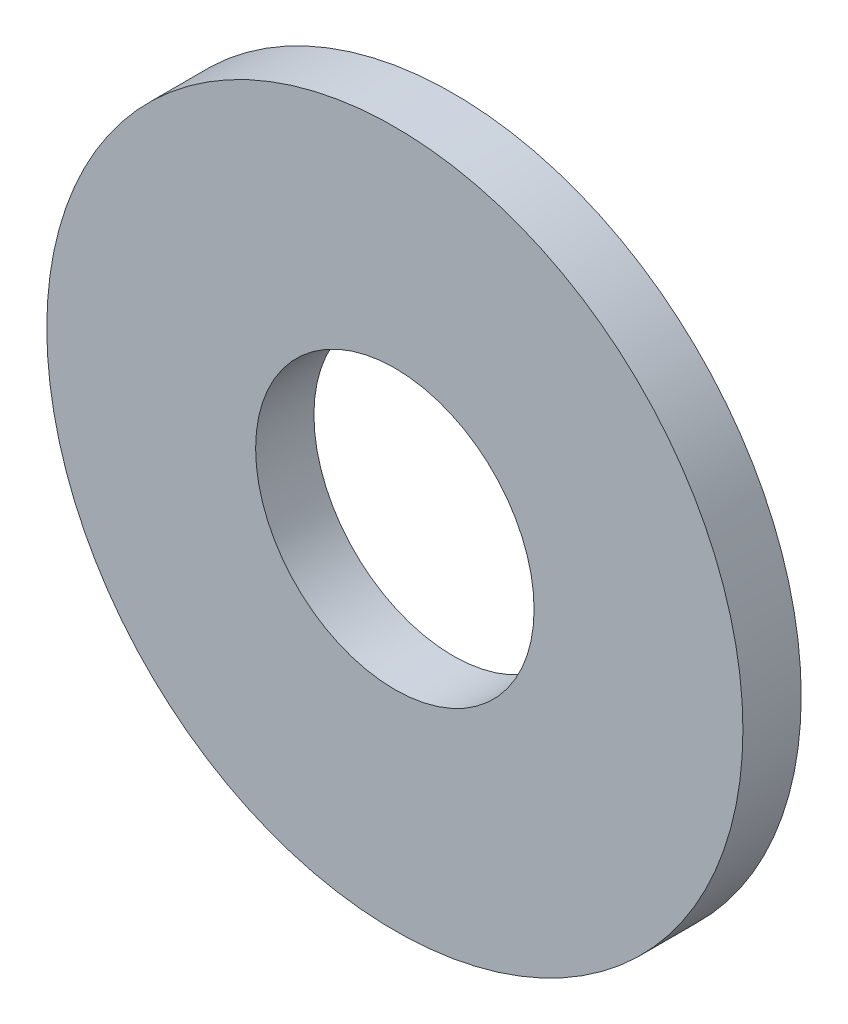
SolidWorks part; units mm, degrees
ref_plane "Front Plane" through (0, 0, 0) normal (0, 0, 1) x (1, 0, 0)
ref_plane "Top Plane" through (0, 0, 0) normal (0, 1, 0) x (1, 0, 0)
ref_plane "Right Plane" through (0, 0, 0) normal (1, 0, 0) x (0, 0, -1)
sketch "Sketch1" plane through (0, 0, 0) normal (0, 0, 1) x (1, 0, 0)
  circle A0 centre (0, 0) radius 1.6
  circle A1 centre (0, 0) radius 4
  dimension "ID" = 3.2
  dimension "OD" = 8
extrude "Extrude1" add sketch "Sketch1" against normal blind 0.67
